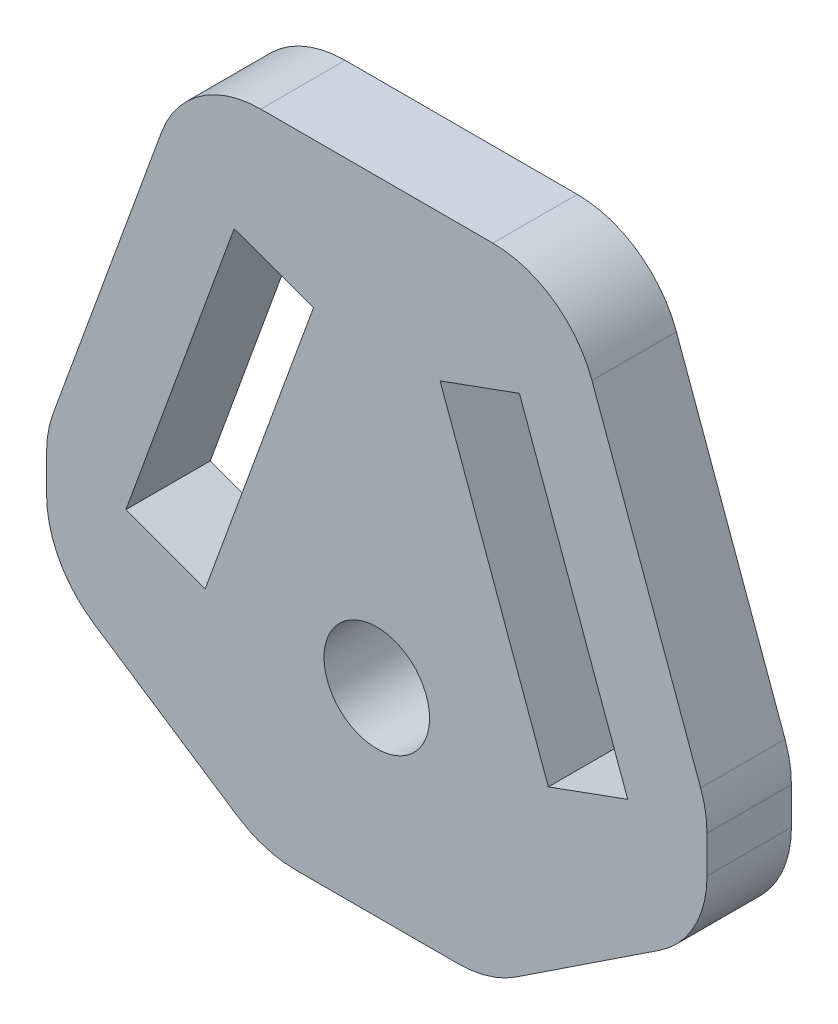
SolidWorks part; units mm, degrees
material "ﾊﾞﾙｻ"
ref_plane "正面" through (0, 0, 0) normal (0, 0, 1) x (1, 0, 0)
ref_plane "平面" through (0, 0, 0) normal (0, 1, 0) x (1, 0, 0)
ref_plane "右側面" through (0, 0, 0) normal (1, 0, 0) x (0, 0, -1)
sketch "ｽｹｯﾁ1" plane through (0, 0, 0) normal (0, 0, 1) x (1, 0, 0)
  line L0 (0, 0) -> (0, 22.8295) construction
  line L1 (-9.0003, 21) -> (-15.6478, 2.7362)
  line L4 (-6.7588, 15.4635) -> (-11.8891, 1.3681)
  line L5 (-11.8891, 1.3681) -> (-8.1303, 0)
  line L6 (-8.1303, 0) -> (-3, 14.0954)
  line L7 (-3, 14.0954) -> (-6.7588, 15.4635)
  line L8 (-12.8009, 0) -> (12.8009, 0) construction
  line L9 (-9.0003, 21) -> (9.0003, 21)
  line L10 (3, 14.0954) -> (6.7588, 15.4635)
  line L11 (8.1303, 0) -> (3, 14.0954)
  line L12 (11.8891, 1.3681) -> (8.1303, 0)
  line L13 (6.7588, 15.4635) -> (11.8891, 1.3681)
  line L16 (9.0003, 21) -> (15.6478, 2.7362)
  line L17 (-15.6478, -7.9056) -> (-11.5505, -9.3969)
  line L18 (-15.6478, 2.7362) -> (-15.6478, -7.9056)
  line L19 (-11.5505, -9.3969) -> (11.5505, -9.3969)
  line L20 (15.6478, 2.7362) -> (15.6478, -7.9056)
  line L21 (15.6478, -7.9056) -> (11.5505, -9.3969)
  line L22 (15.6478, -2.5847) -> (5.3442, -9.3969)
  line L23 (-15.6478, -2.5847) -> (-5.3442, -9.3969)
  circle A0 centre (0, 0) radius 2.5
  point P13 (-13.5992, -8.6513)
  point P16 (0, 21)
  point P27 (0, -9.3969)
  dimension "D1" = 5
  dimension "D6" = 5.3442
  dimension "D2" = 20
  dimension "D3" = 4
  dimension "D4" = 4
  dimension "D5" = 6
  dimension "D8" = 10
  dimension "D10" = 21
  dimension "D11" = 15
extrude "ﾎﾞｽ - 押し出し1" add sketch "ｽｹｯﾁ1" along normal blind 4 contours L18 L23 L19 L22 L20 L16 L9 L1 A0 L7 L6 L5 L4 L10 L13 L12 L11
fillet "ﾌｨﾚｯﾄ1" radius 5 8 edges at (15.6478, 2.7362, 2) (-15.6478, 2.7362, 2) (-9.0003, 21, 2) (9.0003, 21, 2) (-15.6478, -2.5847, 2) (-5.3442, -9.3969, 2) (5.3442, -9.3969, 2) (15.6478, -2.5847, 2)
